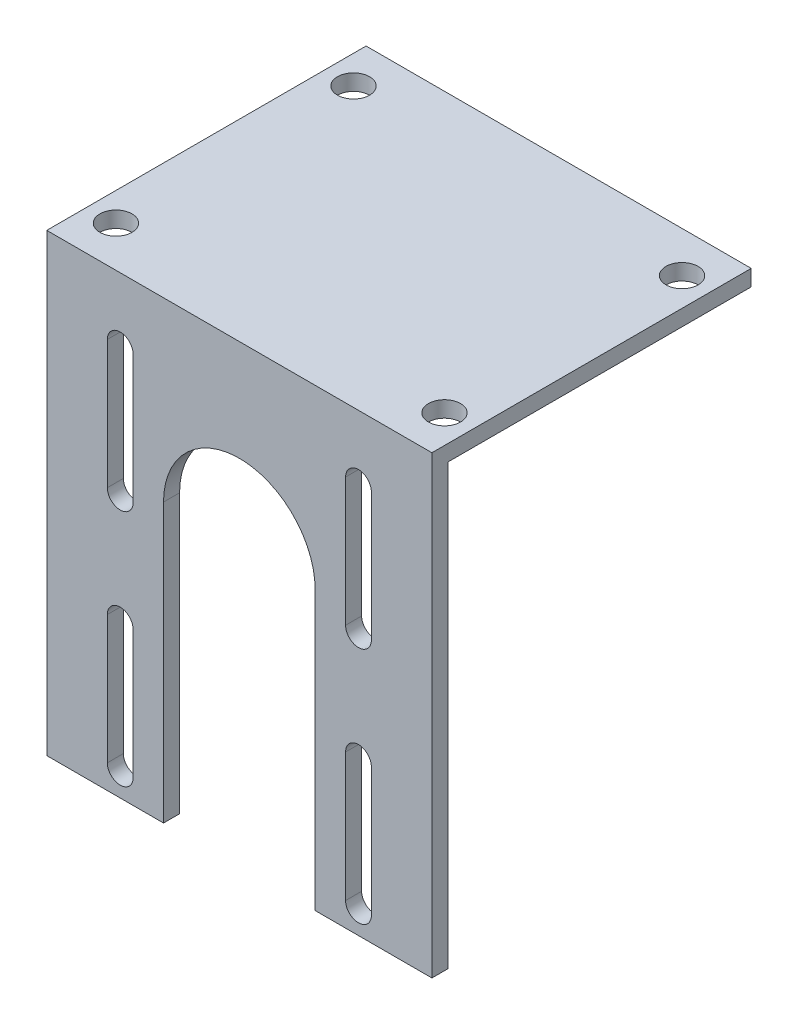
SolidWorks part; units mm, degrees
material "6061 Alloy"
ref_plane "Front Plane" through (0, 0, 0) normal (0, 0, 1) x (1, 0, 0)
ref_plane "Top Plane" through (0, 0, 0) normal (0, 1, 0) x (1, 0, 0)
ref_plane "Right Plane" through (0, 0, 0) normal (1, 0, 0) x (0, 0, -1)
sketch "Sketch1" plane through (0, 0, 0) normal (0, 0, 1) x (1, 0, 0)
  line L2 (0, 0) -> (0, -100)
  line L3 (0, -100) -> (76.2, -100)
  line L9 (76.2, -100) -> (76.2, 0)
  line L10 (0, 0) -> (76.2, 0)
  line L11 (14.53, -25.4) -> (61.67, -25.4) construction
  line L12 (38.1, 0) -> (38.1, -100) construction
  line L14 (14.53, -12.7) -> (14.53, -38.1) construction
  line L15 (61.67, -47.5975) -> (61.67, -25.4) construction
  line L16 (17.08, -12.7) -> (17.08, -38.1)
  line L17 (11.98, -12.7) -> (11.98, -38.1)
  line L18 (61.67, -12.7) -> (61.67, -38.1) construction
  line L19 (59.12, -12.7) -> (59.12, -38.1)
  line L20 (64.22, -12.7) -> (64.22, -38.1)
  line L21 (14.53, -85.24) -> (14.53, -59.84) construction
  line L22 (17.08, -85.24) -> (17.08, -59.84)
  line L23 (11.98, -85.24) -> (11.98, -59.84)
  line L24 (61.67, -85.265) -> (61.67, -59.815) construction
  line L25 (59.12, -85.265) -> (59.12, -59.815)
  line L26 (64.22, -85.265) -> (64.22, -59.815)
  arc A8 (17.08, -12.7) -> (11.98, -12.7) centre (14.53, -12.7) ccw
  arc A9 (11.98, -38.1) -> (17.08, -38.1) centre (14.53, -38.1) ccw
  arc A10 (59.12, -12.7) -> (64.22, -12.7) centre (61.67, -12.7) cw
  arc A11 (64.22, -38.1) -> (59.12, -38.1) centre (61.67, -38.1) cw
  arc A12 (17.08, -85.24) -> (11.98, -85.24) centre (14.53, -85.24) cw
  arc A13 (11.98, -59.84) -> (17.08, -59.84) centre (14.53, -59.84) cw
  arc A14 (59.12, -85.265) -> (64.22, -85.265) centre (61.67, -85.265) ccw
  arc A15 (64.22, -59.815) -> (59.12, -59.815) centre (61.67, -59.815) ccw
  point P16 (38.1, -25.4)
  point P20 (14.53, -25.4)
  point P21 (76.2, -100)
  point P26 (0, 0)
  point P29 (76.2, 0)
  point P31 (61.67, -25.4)
  point P37 (14.53, -72.54)
  point P44 (61.67, -72.54)
  dimension "D3" = 47.14
  dimension "D4" = 47.14
  dimension "D6" = 25.4
  dimension "D5" = 2.55
  dimension "D1" = 76.2
  dimension "D2" = 100
  dimension "D7" = 25.4
  dimension "D8" = 25.45
  dimension "D9" = 25.4
extrude "Boss-Extrude1" add sketch "Sketch1" along normal blind 3.175
sketch "Sketch2" plane through (0, 0, 3.175) normal (0, 0, 1) x (1, 0, 0)
  line L0 (23.1, -35) -> (23.1, -100)
  line L1 (0, -100) -> (76.2, -100) construction
  line L2 (53.1, -35) -> (53.1, -100)
  line L3 (76.2, 0) -> (0, 0) construction
  line L8 (23.1, -100) -> (53.1, -100)
  arc A3 (23.1, -35) -> (53.1, -35) centre (38.1, -35) cw
  point P4 (38.1, 0)
  dimension "D1" = 15
  dimension "D2" = 35
extrude "Cut-Extrude2" cut sketch "Sketch2" against normal up to next
sketch "Sketch4" plane through (0, 0, 0) normal (0, 0, -1) x (-1, 0, 0)
  line L0 (0, 0) -> (0, -100) construction
  line L1 (-76.2, 0) -> (0, 0)
  line L2 (-76.2, 0) -> (-76.2, -3.175)
  line L3 (-76.2, -3.175) -> (0, -3.175)
  line L4 (0, 0) -> (0, -3.175)
  dimension "D1" = 3.175
extrude "Boss-Extrude2" add sketch "Sketch4" along normal blind 60
sketch "Sketch5" plane through (0, 0, 0) normal (0, 1, 0) x (1, 0, 0)
  line L2 (5.6, 51.9125) -> (70.6, 51.9125) construction
  line L3 (70.6, 51.9125) -> (70.6, 4.9125) construction
  line L4 (70.6, 4.9125) -> (5.6, 4.9125) construction
  line L5 (5.6, 4.9125) -> (5.6, 51.9125) construction
  line L6 (38.1, -940) -> (38.1, 49060) construction
  line L7 (0, 60) -> (76.2, 60) construction
  line L8 (-1000, 28.4125) -> (49000, 28.4125) construction
  line L9 (0, -3.175) -> (0, 60) construction
  circle A0 centre (5.6, 51.9125) radius 3.175
  circle A1 centre (5.6, 4.9125) radius 3.175
  circle A2 centre (70.6, 51.9125) radius 3.175
  circle A3 centre (70.6, 4.9125) radius 3.175
  point P13 (38.1, 60)
  point P14 (38.1, 51.9125)
  point P18 (0, 28.4125)
  point P19 (5.6, 28.4125)
  dimension "D1" = 6.35
  dimension "D2" = 65
  dimension "D3" = 47
extrude "Cut-Extrude3" cut sketch "Sketch5" against normal up to surface (3.175 mm away) up to face at (38.1, -3.175, -30)
sketch "Sketch6" plane through (0, 0, 3.175) normal (0, 0, 1) x (1, 0, 0)
  line L5 (0, 0) -> (0, -100) construction
  line L6 (0, -90) -> (76.2, -90)
  line L7 (0, -90) -> (0, -100)
  line L8 (0, -100) -> (76.2, -100)
  line L9 (76.2, -90) -> (76.2, -100)
  dimension "D1" = 10
extrude "Cut-Extrude4" cut sketch "Sketch6" against normal through all
